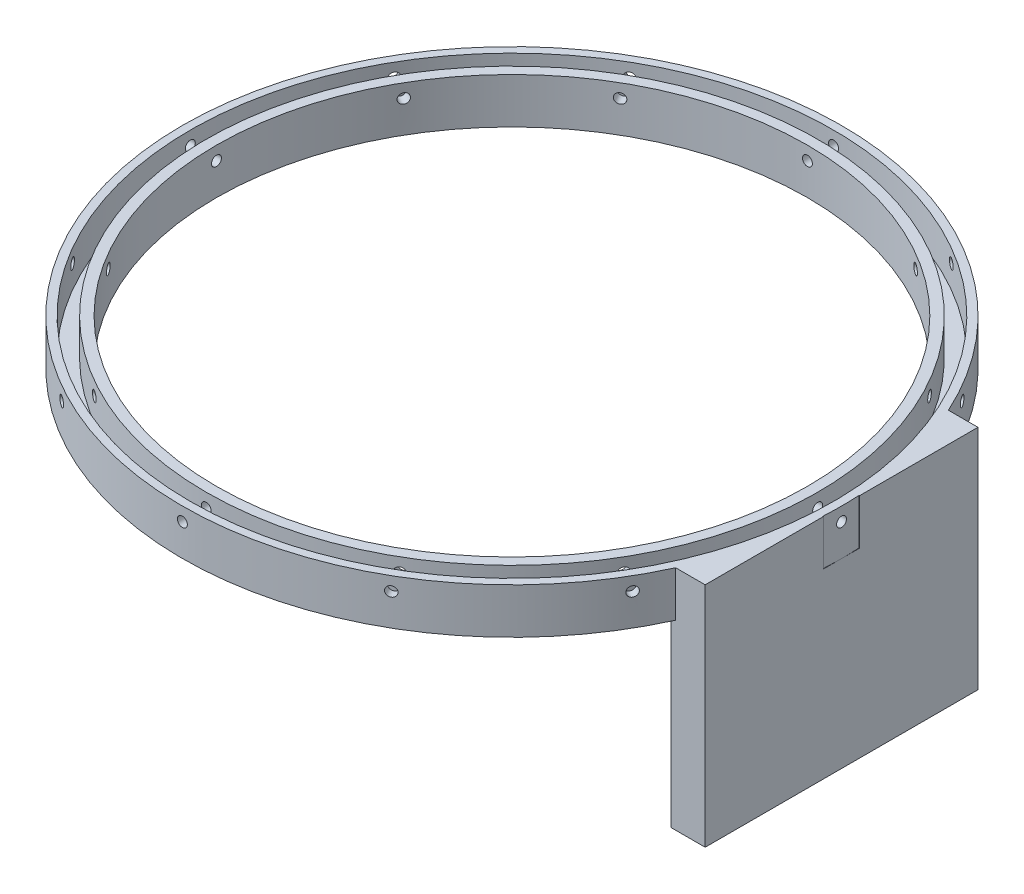
SolidWorks part; units mm, degrees
ref_plane "Front Plane" through (0, 0, 0) normal (0, 0, 1) x (1, 0, 0)
ref_plane "Top Plane" through (0, 0, 0) normal (0, 1, 0) x (1, 0, 0)
ref_plane "Right Plane" through (0, 0, 0) normal (1, 0, 0) x (0, 0, -1)
sketch "Sketch1" plane through (0, 0, 0) normal (0, 1, 0) x (1, 0, 0)
  circle A0 centre (0, 0) radius 92.075
  circle A1 centre (0, 0) radius 82.55
  dimension "D1" = 184.15
  dimension "D2" = 165.1
extrude "Boss-Extrude1" add sketch "Sketch1" along normal blind 12.7
sketch "Sketch2" plane through (0, 12.7, 0) normal (0, 1, 0) x (1, 0, 0)
  circle A0 centre (0, 0) radius 85.4075
  circle A1 centre (0, 0) radius 89.8525
  dimension "D1" = 179.705
  dimension "D2" = 170.815
extrude "Cut-Extrude1" cut sketch "Sketch2" against normal blind 10.16
sketch "Sketch3" plane through (0, 0, 0) normal (0, 0, 1) x (1, 0, 0)
  line L0 (92.075, 12.7) -> (-92.075, 12.7) construction
  circle A0 centre (0, 8.89) radius 1.3843
  dimension "D1" = 2.7686
  dimension "D2" = 3.81
extrude "Cut-Extrude2" cut sketch "Sketch3" against normal up to surface (92.0646 mm away)
pattern_circular "CirPattern1" count 12 over 360 about axis through (0, 12.7, 0) along (0, 1, 0) of "Cut-Extrude2"
sketch "Sketch4" plane through (0, 0, 0) normal (0, -1, 0) x (-1, 0, 0)
  line L0 (0, 0) -> (-92.075, 0) construction
  line L1 (-92.075, 38.1) -> (-82.55, 38.1)
  line L2 (-92.075, 38.1) -> (-92.075, -38.1)
  line L3 (-92.075, -38.1) -> (-82.55, -38.1)
  line L4 (-82.55, 38.1) -> (-82.55, -38.1)
  circle A0 centre (0, 0) radius 82.55 construction
  circle A1 centre (0, 0) radius 92.075 construction
  dimension "D1" = 38.1
  dimension "D2" = 76.2
extrude "Boss-Extrude2" add sketch "Sketch4" along normal blind 50.8
sketch "Sketch5" plane through (0, 0, 0) normal (0, 1, 0) x (1, 0, 0)
  line L0 (92.075, -5.08) -> (91.9348, -5.08)
  line L1 (92.075, 5.08) -> (91.9348, 5.08)
  line L2 (92.075, 0) -> (92.075, 38.1)
  line L3 (92.075, 38.1) -> (83.8224, 38.1)
  line L4 (92.075, 5.08) -> (92.075, 38.1)
  line L5 (92.075, 38.1) -> (83.8224, 38.1)
  line L6 (83.8224, -38.1) -> (92.075, -38.1)
  line L7 (92.075, -38.1) -> (92.075, 0)
  line L8 (83.8224, -38.1) -> (92.075, -38.1)
  line L9 (92.075, -38.1) -> (92.075, -5.08)
  arc A1 (92.075, 0) -> (83.8224, 38.1) centre (0, 0) ccw
  arc A2 (91.9348, 5.08) -> (83.8224, 38.1) centre (0, 0) ccw
  arc A3 (83.8224, -38.1) -> (92.075, 0) centre (0, 0) ccw
  arc A4 (83.8224, -38.1) -> (91.9348, -5.08) centre (0, 0) ccw
  dimension "D3" = 5.08
  dimension "D4" = 5.08
  dimension "D1" = 0
  dimension "D2" = 0
extrude "Boss-Extrude4" add sketch "Sketch5" along normal up to surface (12.7 mm away) up to face at (0, 12.7, 89.8525)
